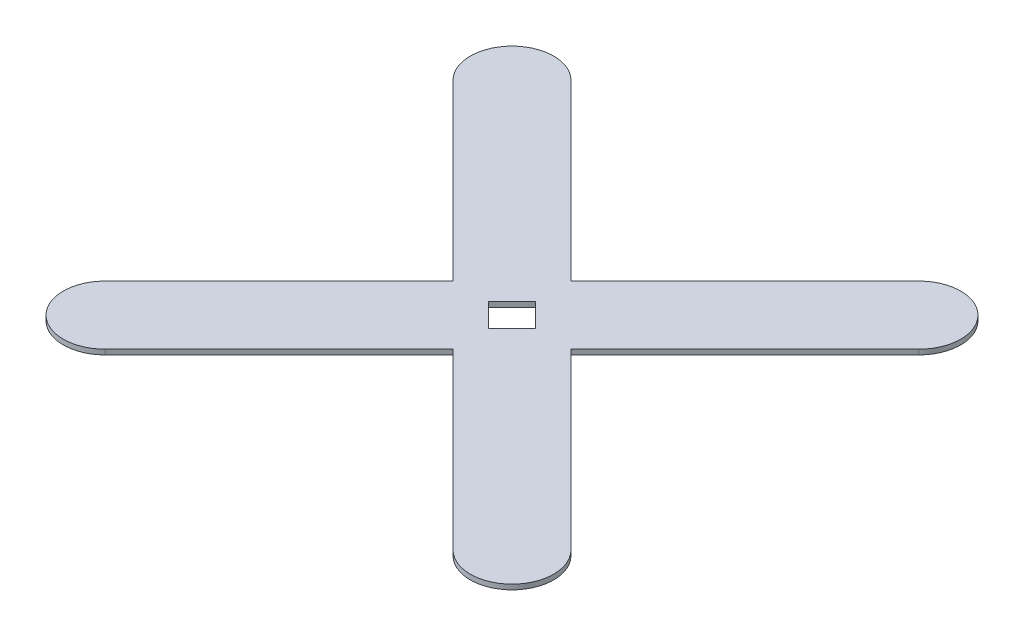
SolidWorks part; units mm, degrees
ref_plane "Front Plane" through (0, 0, 0) normal (0, 0, 1) x (1, 0, 0)
ref_plane "Top Plane" through (0, 0, 0) normal (0, 1, 0) x (1, 0, 0)
ref_plane "Right Plane" through (0, 0, 0) normal (1, 0, 0) x (0, 0, -1)
sketch "Sketch2" plane through (0, 0, 0) normal (0, 1, 0) x (1, 0, 0)
  line L0 (122, -122) -> (-122, 122) construction
  line L1 (-147, -147) -> (147, -147) construction
  line L2 (-147, -147) -> (-147, 147) construction
  line L3 (-147, 147) -> (147, 147) construction
  line L4 (147, -147) -> (147, 147) construction
  line L5 (-147, -147) -> (147, 147) construction
  line L6 (-147, 147) -> (147, -147) construction
  line L7 (104.3223, -139.6777) -> (0, -35.3553)
  line L8 (139.6777, -104.3223) -> (35.3553, 0)
  line L9 (-122, -122) -> (122, 122) construction
  line L10 (-139.6777, -104.3223) -> (-35.3553, 0)
  line L11 (-104.3223, -139.6777) -> (0, -35.3553)
  line L12 (0, 35.3553) -> (104.3223, 139.6777)
  line L13 (35.3553, 0) -> (139.6777, 104.3223)
  line L14 (-35.3553, 0) -> (-139.6777, 104.3223)
  line L15 (0, 35.3553) -> (-104.3223, 139.6777)
  line L17 (-147, 147) -> (-47, 147) construction
  line L18 (-147, 147) -> (-147, 47) construction
  line L21 (-147, 0) -> (147, 0) construction
  arc A0 (104.3223, -139.6777) -> (139.6777, -104.3223) centre (122, -122) ccw
  arc A1 (-104.3223, 139.6777) -> (-139.6777, 104.3223) centre (-122, 122) ccw
  arc A2 (-139.6777, -104.3223) -> (-104.3223, -139.6777) centre (-122, -122) ccw
  arc A3 (139.6777, 104.3223) -> (104.3223, 139.6777) centre (122, 122) ccw
  point P0 (0, 0)
  point P8 (0, 0)
  point P15 (0, 0)
extrude "Boss-Extrude2" add sketch "Sketch2" along normal blind 3
sketch "Sketch6" plane through (0, 3, 0) normal (0, 1, 0) x (1, 0, 0)
  line L1 (0, -14.1421) -> (14.1421, 0)
  line L2 (0, -14.1421) -> (-14.1421, 0)
  line L3 (-14.1421, 0) -> (0, 14.1421)
  line L4 (14.1421, 0) -> (0, 14.1421)
  line L5 (0, -14.1421) -> (0, 14.1421) construction
  line L6 (-14.1421, 0) -> (14.1421, 0) construction
  point P0 (0, 0)
extrude "Cut-Extrude2" cut sketch "Sketch6" against normal blind 5
